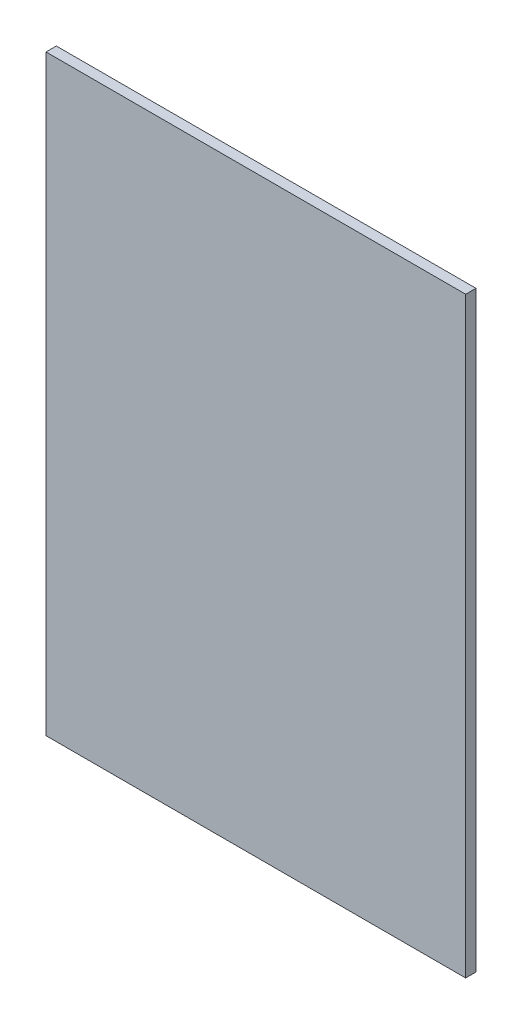
SolidWorks part; units mm, degrees
ref_plane "Front Plane" through (0, 0, 0) normal (0, 0, 1) x (1, 0, 0)
ref_plane "Top Plane" through (0, 0, 0) normal (0, 1, 0) x (1, 0, 0)
ref_plane "Right Plane" through (0, 0, 0) normal (1, 0, 0) x (0, 0, -1)
sketch "Sketch1" plane through (0, 0, 0) normal (0, 0, 1) x (1, 0, 0)
  line L1 (-103.505, 146.05) -> (103.505, 146.05)
  line L2 (-103.505, 146.05) -> (-103.505, -146.05)
  line L3 (-103.505, -146.05) -> (103.505, -146.05)
  line L4 (103.505, 146.05) -> (103.505, -146.05)
  line L5 (-103.505, 146.05) -> (103.505, -146.05) construction
  line L6 (-103.505, -146.05) -> (103.505, 146.05) construction
  point P0 (0, 0)
  dimension "D1" = 207.01
  dimension "D2" = 292.1
extrude "Boss-Extrude1" add sketch "Sketch1" along normal mid plane 5.08
